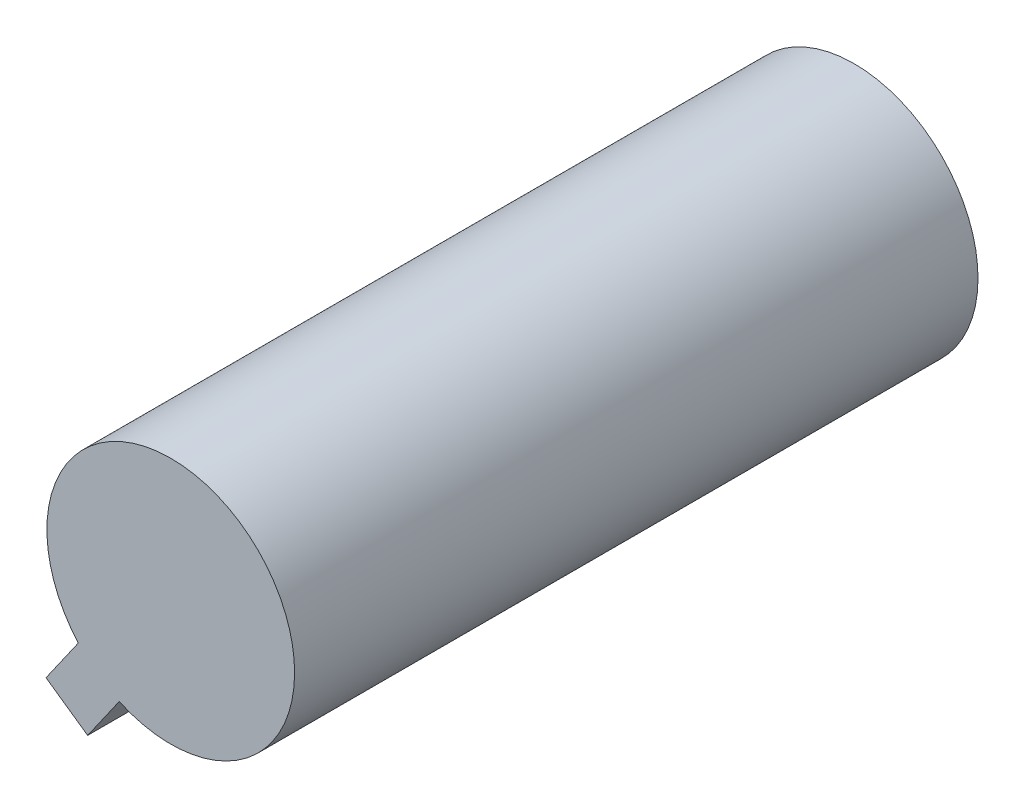
SolidWorks part; units mm, degrees
ref_plane "Front Plane" through (0, 0, 0) normal (0, 0, 1) x (1, 0, 0)
ref_plane "Top Plane" through (0, 0, 0) normal (0, 1, 0) x (1, 0, 0)
ref_plane "Right Plane" through (0, 0, 0) normal (1, 0, 0) x (0, 0, -1)
sketch "Sketch1" plane through (0, 0, 0) normal (0, 0, 1) x (1, 0, 0)
  circle A0 centre (0, 0) radius 7
  dimension "D1" = 14
extrude "Boss-Extrude1" add sketch "Sketch1" along normal blind 38.63
ref_plane "Plane1" through (-4.0139, -5.7349, 0) normal (-0.5734, -0.8193, 0) x (-0.8193, 0.5734, 0)
sketch "Sketch2" plane through (-4.0139, -5.7349, 0) normal (-0.5734, -0.8193, 0) x (-0.8193, 0.5734, 0)
  line L0 (7, 0) -> (-7, 0) construction
  line L1 (-1.2646, 0) -> (1.6083, 0)
  line L2 (-1.2646, 0) -> (-1.2646, -13.2033)
  line L3 (-1.2646, -13.2033) -> (1.6083, -13.2033)
  line L4 (1.6083, 0) -> (1.6083, -13.2033)
  line L5 (7.5, -38.63) -> (-7.5, -38.63) construction
  line L6 (-1.2646, -38.63) -> (1.6083, -38.63)
  line L7 (-1.2646, -38.63) -> (-1.2646, -24.9613)
  line L8 (-1.2646, -24.9613) -> (1.6083, -24.9613)
  line L9 (1.6083, -38.63) -> (1.6083, -24.9613)
extrude "Boss-Extrude2" add sketch "Sketch2" along normal blind 3 separate body
sketch "Sketch3" plane through (-4.0139, -5.7349, 0) normal (0.5734, 0.8193, 0) x (0.8193, -0.5734, 0)
  line L1 (-1.6083, -24.9613) -> (1.2646, -24.9613)
  line L2 (-1.6083, -24.9613) -> (-1.6083, -38.63)
  line L3 (-1.6083, -38.63) -> (1.2646, -38.63)
  line L4 (1.2646, -24.9613) -> (1.2646, -38.63)
  line L5 (1.2646, 0) -> (-1.6083, 0)
  line L6 (1.2646, 0) -> (1.2646, -13.2033)
  line L7 (1.2646, -13.2033) -> (-1.6083, -13.2033)
  line L8 (-1.6083, 0) -> (-1.6083, -13.2033)
extrude "Boss-Extrude3" add sketch "Sketch3" along normal blind 10
